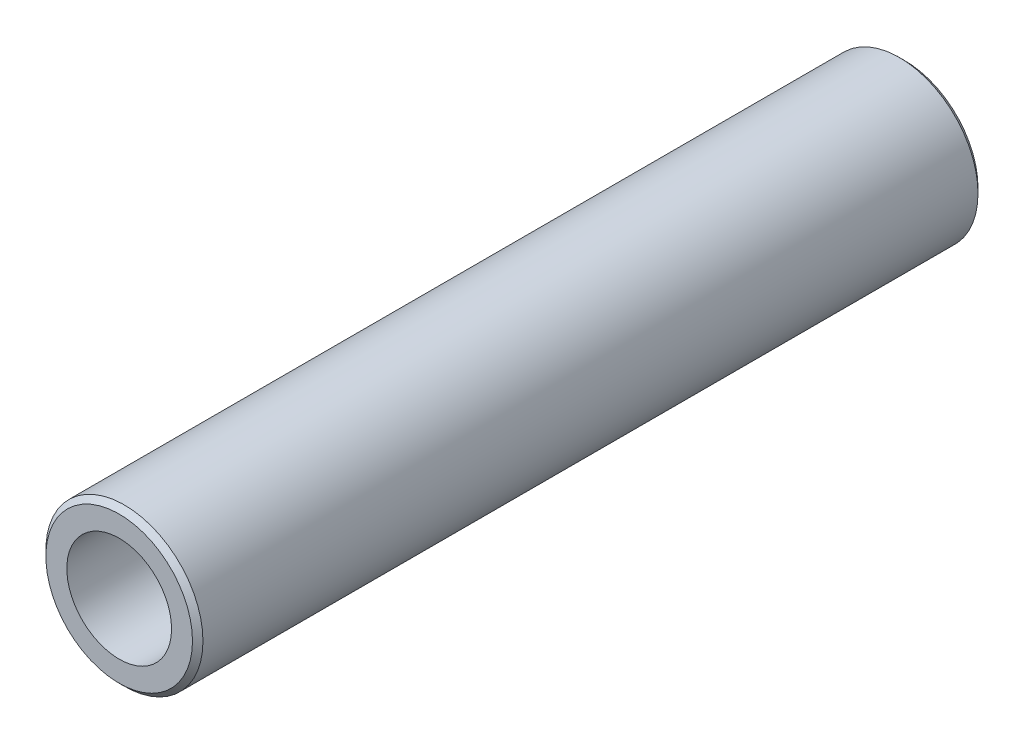
SolidWorks part; units mm, degrees
ref_plane "Спереди" through (0, 0, 0) normal (0, 0, 1) x (1, 0, 0)
ref_plane "Сверху" through (0, 0, 0) normal (0, 1, 0) x (1, 0, 0)
ref_plane "Справа" through (0, 0, 0) normal (1, 0, 0) x (0, 0, -1)
sketch "Эскиз1" plane through (0, 0, 0) normal (0, 0, 1) x (1, 0, 0)
  circle A0 centre (0, 0) radius 3
  dimension "D1" = 6
extrude "Бобышка-Вытянуть1" add sketch "Эскиз1" along normal blind 30
sketch "Эскиз2" plane through (0, 0, 30) normal (0, 0, 1) x (1, 0, 0)
  circle A0 centre (0, 0) radius 1
extrude "Вырез-Вытянуть1" cut sketch "Эскиз2" against normal blind 30
sketch "Эскиз3" plane through (0, 0, 30) normal (0, 0, 1) x (1, 0, 0)
  circle A0 centre (0, 0) radius 2
extrude "Вырез-Вытянуть2" cut sketch "Эскиз3" against normal blind 20
chamfer "Фаска1" distance 1 angle 45 1 edges at (1, 0, 0)
chamfer "Фаска2" distance 0.2 angle 45 2 edges at (3, 0, 30) (3, 0, 0)
